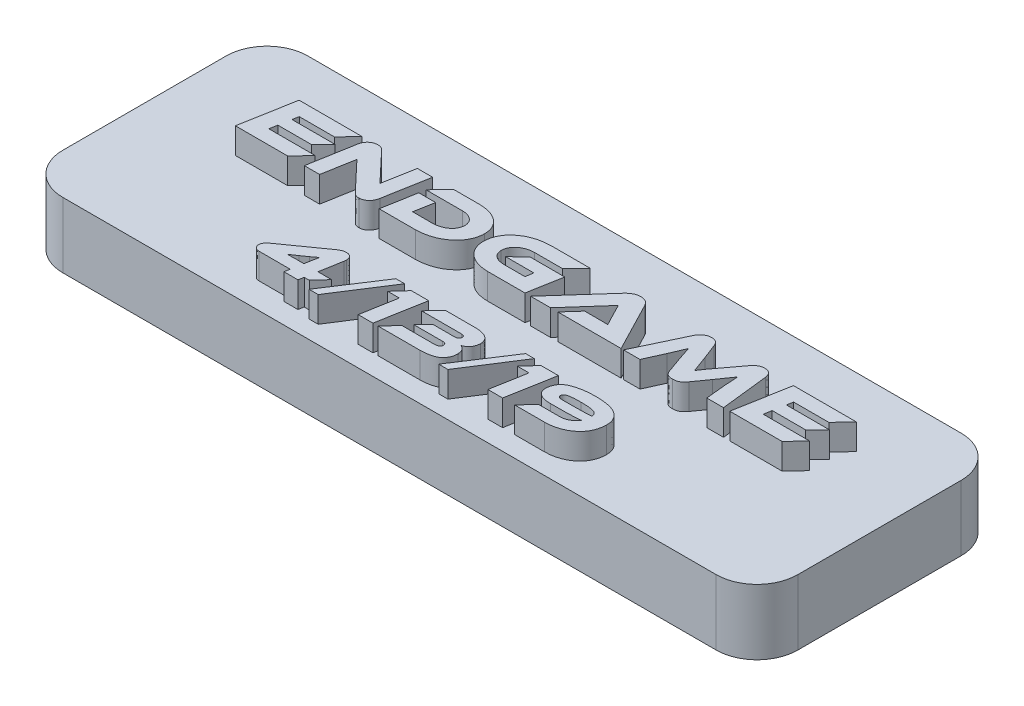
SolidWorks part; units mm, degrees
ref_plane "Front Plane" through (0, 0, 0) normal (0, 0, 1) x (1, 0, 0)
ref_plane "Top Plane" through (0, 0, 0) normal (0, 1, 0) x (1, 0, 0)
ref_plane "Right Plane" through (0, 0, 0) normal (1, 0, 0) x (0, 0, -1)
sketch "Sketch1" plane through (0, 0, 0) normal (0, 1, 0) x (1, 0, 0)
  line L1 (-28.575, 9.525) -> (28.575, 9.525)
  line L2 (-28.575, 9.525) -> (-28.575, -9.525)
  line L3 (-28.575, -9.525) -> (28.575, -9.525)
  line L4 (28.575, 9.525) -> (28.575, -9.525)
  line L5 (-28.575, 9.525) -> (28.575, -9.525) construction
  line L6 (-28.575, -9.525) -> (28.575, 9.525) construction
  point P0 (0, 0)
  dimension "D1" = 57.15
  dimension "D2" = 19.05
extrude "Boss-Extrude1" add sketch "Sketch1" along normal up to surface (5.08 mm away)
fillet "Fillet1" radius 3.175 4 edges at (-28.575, 2.54, 9.525) (-28.575, 2.54, -9.525) (28.575, 2.54, 9.525) (28.575, 2.54, -9.525)
sketch "Sketch3" plane through (0, 5.08, 0) normal (0, 1, 0) x (1, 0, 0)
  line L0 (28.575, -7.9375) -> (-28.575, -7.9375) construction
  line L1 (28.575, -6.35) -> (28.575, 6.35) construction
  line L2 (-28.575, 6.35) -> (-28.575, -6.35) construction
  line L3 (28.575, 0) -> (-28.575, 0) construction
  line L5 (-25.4, -9.525) -> (25.4, -9.525) construction
  line L6 (25.4, 9.525) -> (-25.4, 9.525) construction
  text T0 "ENDGAME" font "Ethnocentric Rg" height in points 16
  text T1 "4/13/19" font "Ethnocentric Rg" height in points 14
  point P8 (-28.575, 0)
  dimension "D1" = 1.5875
extrude "Boss-Extrude2" add sketch "Sketch3" along normal blind 2
sketch "Sketch4" plane through (0, 0, 0) normal (0, -1, 0) x (1, 0, 0)
  line L0 (25.4, 0) -> (-25.4, 0) construction
  circle A0 centre (-25.4, 0) radius 0.9
  circle A1 centre (25.4, 0) radius 0.9
  point P3 (0, 0)
  dimension "D2" = 1.8
  dimension "D1" = 50.8
extrude "Cut-Extrude1" cut sketch "Sketch4" against normal blind 4
